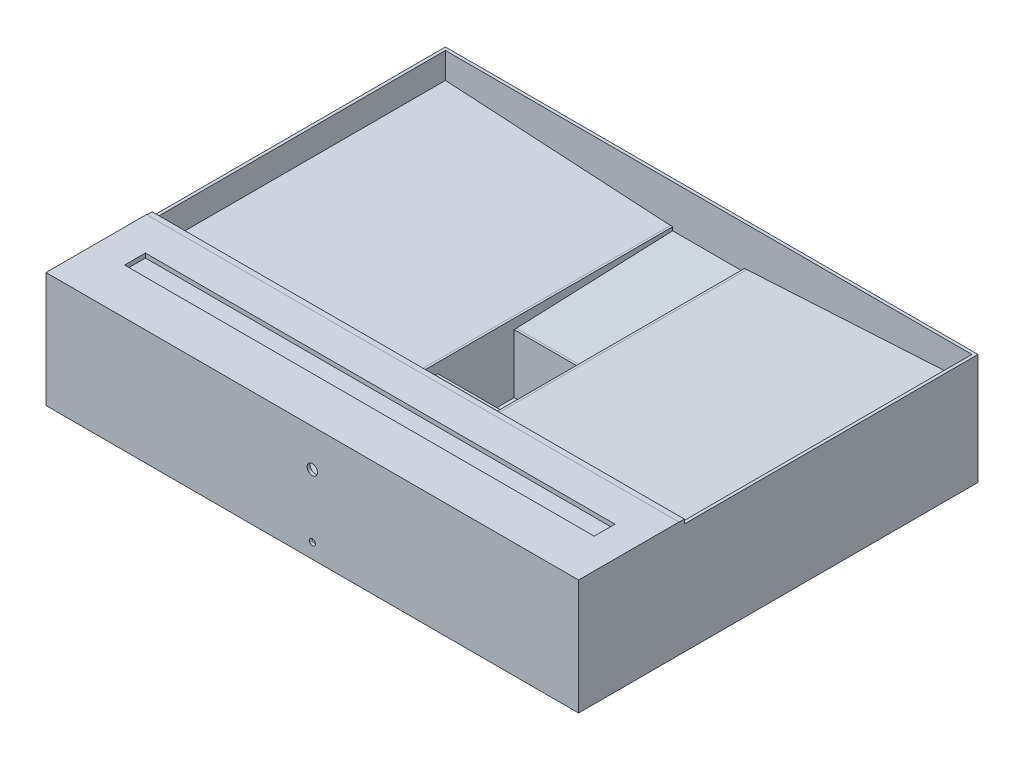
SolidWorks part; units mm, degrees
material "Pine"
ref_plane "Front Plane" through (0, 0, 0) normal (0, 0, 1) x (1, 0, 0)
ref_plane "Top Plane" through (0, 0, 0) normal (0, 1, 0) x (1, 0, 0)
ref_plane "Right Plane" through (0, 0, 0) normal (1, 0, 0) x (0, 0, -1)
sketch "Sketch1" plane through (0, 0, 0) normal (0, 1, 0) x (1, 0, 0)
  line L1 (-610, -457.5) -> (610, -457.5)
  line L2 (-610, -457.5) -> (-610, 457.5)
  line L3 (-610, 457.5) -> (610, 457.5)
  line L4 (610, -457.5) -> (610, 457.5)
  line L5 (-610, -457.5) -> (610, 457.5) construction
  line L6 (-610, 457.5) -> (610, -457.5) construction
  point P0 (0, 0)
  dimension "D1" = 1220
  dimension "D2" = 915
extrude "Boss-Extrude1" add sketch "Sketch1" along normal blind 254
shell "Shell1" thickness 7
sketch "Sketch2" plane through (0, 0, -450.5) normal (0, 0, 1) x (1, 0, 0)
  line L0 (-603, 254) -> (-603, 194.5145) construction
  line L1 (-603, 254) -> (-603, 7) construction
  line L2 (0, 254) -> (0, 164.5145) construction
  line L3 (603, 254) -> (-603, 254) construction
  line L4 (-87.5, 164.5145) -> (87.5, 164.5145) construction
  line L5 (-87.5, 164.5145) -> (-603, 194.5145)
  line L6 (-603, 194.5145) -> (-603, 186.5145)
  line L7 (-87.5, 164.5145) -> (-87.5, 156.5145)
  line L8 (-87.5, 156.5145) -> (-603, 186.5145)
  line L9 (603, 254) -> (603, 194) construction
  line L10 (603, 254) -> (603, 7) construction
  line L11 (603, 194) -> (87.5, 164.5145)
  line L12 (87.5, 164.5145) -> (87.5, 156.5145)
  line L13 (603, 194) -> (603, 186)
  line L14 (603, 186) -> (87.5, 156.5145)
  point P13 (0, 164.5145)
extrude "Boss-Extrude2" add sketch "Sketch2" along normal up to surface (901 mm away) up to face at (0, 130.5, 450.5)
sketch "Sketch3" plane through (0, 7, 0) normal (0, 1, 0) x (1, 0, 0)
  line L0 (-82.5, 87.5) -> (-82.5, -87.5)
  line L1 (87.5, -450.5) -> (87.5, 450.5) construction
  line L2 (87.5, -92.5) -> (87.5, 92.5)
  line L3 (87.5, 92.5) -> (-87.5, 92.5)
  line L4 (-87.5, -450.5) -> (-87.5, 450.5) construction
  line L5 (-87.5, 92.5) -> (-87.5, -92.5)
  line L6 (-87.5, -92.5) -> (87.5, -92.5)
  line L7 (-82.5, -87.5) -> (82.5, -87.5)
  line L8 (82.5, -87.5) -> (82.5, 87.5)
  line L9 (82.5, 87.5) -> (-82.5, 87.5)
  point P6 (0, 0)
  point P10 (87.5, 0)
  dimension "D1" = 5
extrude "Boss-Extrude3" add sketch "Sketch3" along normal blind 135
sketch "Sketch4" plane through (87.5, 0, 0) normal (-1, 0, 0) x (0, 0, 1)
  line L0 (92.5, 142) -> (450.5, 156.5145)
  line L1 (450.5, 156.5145) -> (450.5, 151.5145)
  line L2 (450.5, 186) -> (450.5, 7) construction
  line L3 (92.5, 142) -> (92.5, 137)
  line L4 (92.5, 142) -> (92.5, 7) construction
  line L5 (92.5, 137) -> (450.5, 151.5145)
  line L6 (-92.5, 142) -> (-450.5, 156.5145)
  line L7 (-450.5, 156.5145) -> (-450.5, 151.5145)
  line L8 (-450.5, 186) -> (-450.5, 7) construction
  line L9 (-92.5, 142) -> (-92.5, 137)
  line L10 (-92.5, 137) -> (-450.5, 151.5145)
extrude "Boss-Extrude4" add sketch "Sketch4" along normal up to surface (175 mm away) up to face at (-87.5, 160.5145, 0)
sketch "Sketch5" plane through (-87.5, 0, 0) normal (1, 0, 0) x (0, 0, -1)
  line L0 (450.5, 164.5145) -> (450.5, 156.5145)
  line L1 (450.5, 156.5145) -> (92.5, 142)
  line L2 (92.5, 142) -> (-92.5, 142)
  line L3 (-92.5, 142) -> (-450.5, 156.5145)
  line L4 (-450.5, 156.5145) -> (-450.5, 164.5145)
  line L5 (-450.5, 164.5145) -> (450.5, 164.5145)
extrude "Boss-Extrude5" add sketch "Sketch5" along normal blind 5
sketch "Sketch6" plane through (87.5, 0, 0) normal (-1, 0, 0) x (0, 0, 1)
  line L0 (450.5, 164.5145) -> (450.5, 156.5145)
  line L1 (450.5, 156.5145) -> (92.5, 142)
  line L2 (92.5, 142) -> (-92.5, 142)
  line L3 (-92.5, 142) -> (-450.5, 156.5145)
  line L4 (-450.5, 156.5145) -> (-450.5, 164.5145)
  line L5 (-450.5, 164.5145) -> (450.5, 164.5145)
extrude "Boss-Extrude6" add sketch "Sketch6" along normal blind 5
sketch "Sketch7" plane through (0, 254, 0) normal (0, 1, 0) x (1, 0, 0)
  line L0 (610, -457.5) -> (610, 457.5) construction
  line L1 (-610, -457.5) -> (610, -457.5)
  line L2 (-610, -457.5) -> (-610, -450.5)
  line L3 (-610, -450.5) -> (610, -450.5)
  line L4 (610, -457.5) -> (610, -450.5)
extrude "Boss-Extrude7" add sketch "Sketch7" along normal blind 320
sketch "Sketch8" plane through (0, 0, 450.5) normal (0, 0, -1) x (-1, 0, 0)
  line L1 (653.4241, 605.862) -> (-694.6909, 605.862)
  line L2 (653.4241, 605.862) -> (653.4241, 255.2773)
  line L3 (653.4241, 255.2773) -> (-694.6909, 255.2773)
  line L4 (-694.6909, 605.862) -> (-694.6909, 255.2773)
extrude "Cut-Extrude1" cut sketch "Sketch8" against normal through all
sketch "Sketch9" plane through (0, 0, 457.5) normal (0, 0, 1) x (1, 0, 0)
  line L0 (-610, 0) -> (610, 0) construction
  circle A0 centre (0, 34) radius 7
  dimension "D1" = 14
  dimension "D2" = 34
extrude "Cut-Extrude2" cut sketch "Sketch9" against normal blind 10 contours A0
sketch "Sketch10" plane through (0, 254, 0) normal (0, 1, 0) x (1, 0, 0)
  line L0 (-610, 457.5) -> (-610, -450.5) construction
  line L1 (610, -457.5) -> (-610, -457.5)
  line L2 (610, -457.5) -> (610, -227.5)
  line L3 (610, -227.5) -> (-610, -227.5)
  line L4 (-610, -457.5) -> (-610, -227.5)
  line L5 (0, -457.5) -> (0, -227.5) construction
  dimension "D1" = 230
extrude "Boss-Extrude8" add sketch "Sketch10" along normal blind 10
ref_plane "Plane1" through (0, 199, 0) normal (0, -1, 0) x (-1, 0, 0)
sketch "Sketch12" plane through (0, 199, 0) normal (0, -1, 0) x (-1, 0, 0)
  line L1 (603, -227.5) -> (-603, -227.5)
  line L2 (603, -227.5) -> (603, -450.5)
  line L3 (603, -450.5) -> (-603, -450.5)
  line L4 (-603, -227.5) -> (-603, -450.5)
  line L5 (610, -457.5) -> (-610, -457.5) construction
  dimension "D1" = 7
extrude "Boss-Extrude10" add sketch "Sketch12" against normal blind 10
sketch "Sketch14" plane through (610, 0, 0) normal (1, 0, 0) x (0, 0, -1)
  line L1 (-229.2038, 263.6907) -> (-215.2089, 263.6907)
  line L2 (-229.2038, 263.6907) -> (-229.2038, 197.4445)
  line L3 (-229.2038, 197.4445) -> (-215.2089, 197.4445)
  line L4 (-215.2089, 263.6907) -> (-215.2089, 197.4445)
extrude "Boss-Extrude13" add sketch "Sketch14" against normal blind 1219.2
sketch "Sketch15" plane through (0, 264, 0) normal (0, 1, 0) x (1, 0, 0)
  line L1 (540.979, -352.6971) -> (-534.7914, -352.6971)
  line L2 (540.979, -352.6971) -> (540.979, -304.9637)
  line L3 (540.979, -304.9637) -> (-534.7914, -304.9637)
  line L4 (-534.7914, -352.6971) -> (-534.7914, -304.9637)
extrude "Cut-Extrude3" cut sketch "Sketch15" against normal blind 10
sketch "Sketch16" plane through (0, 0, 457.5) normal (0, 0, 1) x (1, 0, 0)
  circle A0 centre (0, 177.9726) radius 11.8924
extrude "Cut-Extrude4" cut sketch "Sketch16" against normal blind 10 contours A0
